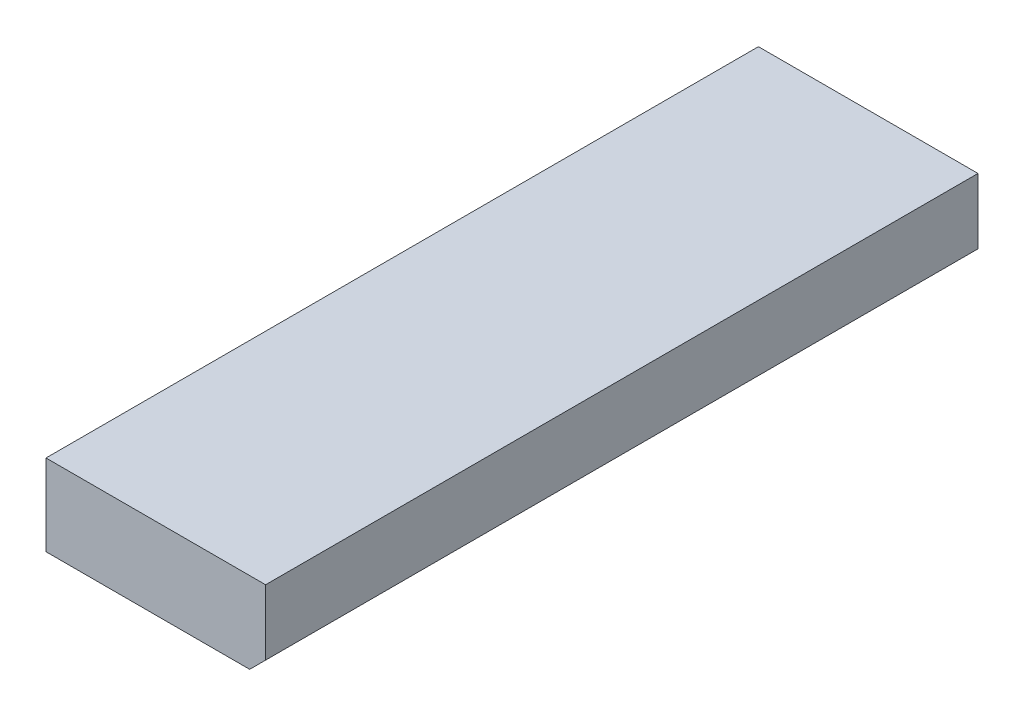
SolidWorks part; units mm, degrees
ref_plane "Top Plane" through (0, 0, 0) normal (0, 0, 1) x (1, 0, 0)
ref_plane "Front Plane" through (0, 0, 0) normal (0, 1, 0) x (1, 0, 0)
ref_plane "Right Plane" through (0, 0, 0) normal (1, 0, 0) x (0, 0, -1)
sketch "Sketch1" plane through (0, 0, 0) normal (0, 0, 1) x (1, 0, 0)
  line L0 (0, 0) -> (0.6112, 0)
  line L1 (55, 0) -> (-55, 0) construction
  line L3 (0.659, 0.2438) -> (0.659, 0.0478)
  line L6 (0, -55) -> (0, 55) construction
  line L7 (0, 0.2438) -> (0, 0)
  line L8 (0.6112, 0) -> (0.659, 0.0478)
  line L9 (0, 0.2438) -> (0.659, 0.2438)
  point P6 (0.659, 0.2438)
  point P8 (0.659, 0.2391)
  dimension "D1" = 0.659
  dimension "D2" = 45
  dimension "D3" = 0.0478
  dimension "D4" = 0.2437
extrude "Boss-Extrude1" add sketch "Sketch1" along normal blind 2.138
